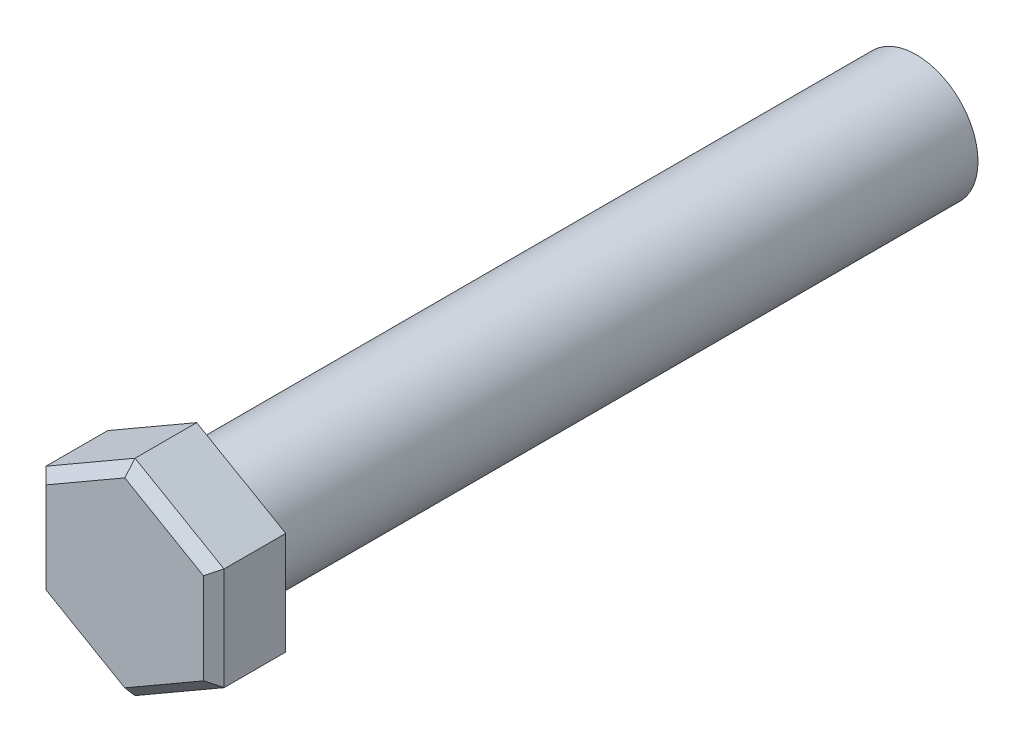
SolidWorks part; units mm, degrees
ref_plane "Alzado" through (0, 0, 0) normal (0, 0, 1) x (1, 0, 0)
ref_plane "Planta" through (0, 0, 0) normal (0, 1, 0) x (1, 0, 0)
ref_plane "Vista lateral" through (0, 0, 0) normal (1, 0, 0) x (0, 0, -1)
sketch "Croquis1" plane through (0, 0, 0) normal (0, 0, 1) x (1, 0, 0)
  circle A0 centre (0, 0) radius 6
  dimension "D1" = 12
extrude "Saliente-Extruir3" add sketch "Croquis1" along normal blind 70
sketch "Croquis3" plane through (0, 0, 70) normal (0, 0, 1) x (1, 0, 0)
  line L0 (0, 0) -> (0, 2.1215)
  line L1 (0, 10) -> (-8.6603, 5)
  line L2 (-8.6603, 5) -> (-8.6603, -5)
  line L3 (-8.6603, -5) -> (0, -10)
  line L4 (0, -10) -> (8.6603, -5)
  line L5 (8.6603, -5) -> (8.6603, 5)
  line L6 (8.6603, 5) -> (0, 10)
  line L7 (0, 2.1215) -> (0, 0)
  line L9 (10, 0) -> (8.6603, 0)
  line L11 (-8.6603, 0) -> (-10, 0)
  arc A0 (-6.141, -7.8923) -> (0, -10) centre (0, 0) ccw
  dimension "D1" = 20
extrude "Saliente-Extruir4" add sketch "Croquis3" along normal blind 7
chamfer "Chaflán1" distance 1 angle 45 6 edges at (8.6603, 0, 77) (4.3301, -7.5, 77) (-4.3301, -7.5, 77) (-8.6603, 0, 77) (-4.3301, 7.5, 77) (4.3301, 7.5, 77)
fillet "Redondeo1" radius 1 1 edges at (6, 0, 70)
